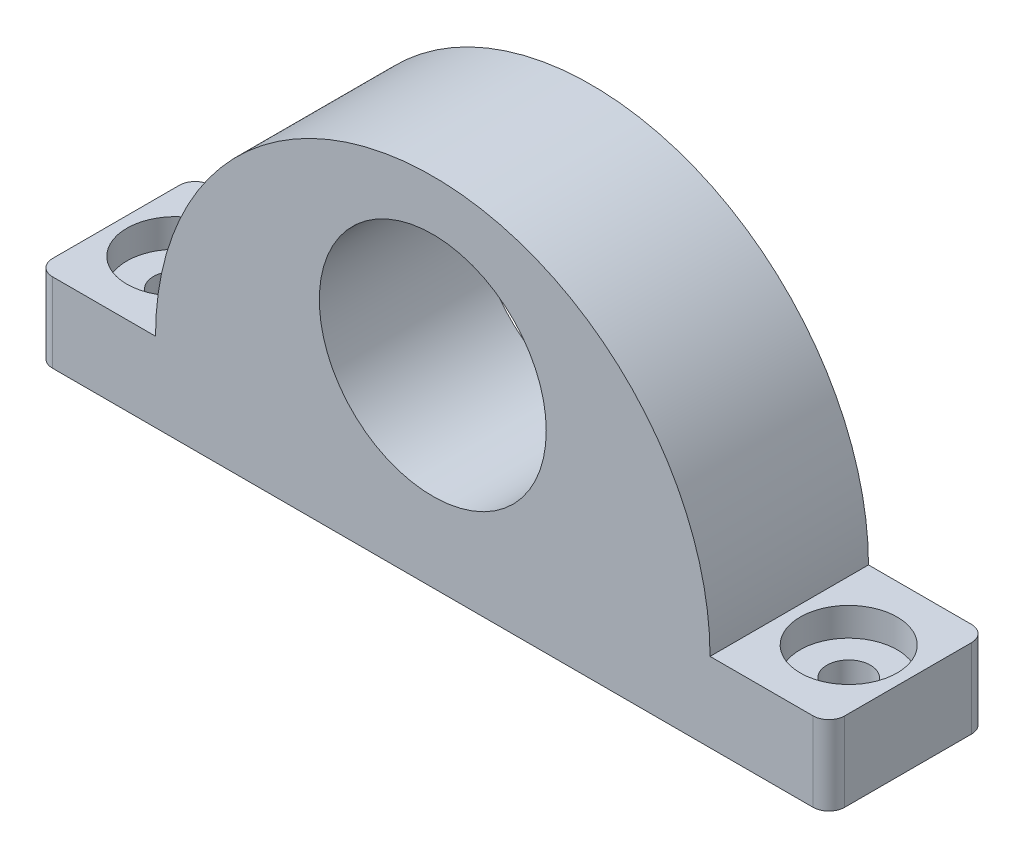
SolidWorks part; units mm, degrees
ref_plane "Front Plane" through (0, 0, 0) normal (0, 0, 1) x (1, 0, 0)
ref_plane "Top Plane" through (0, 0, 0) normal (0, 1, 0) x (1, 0, 0)
ref_plane "Right Plane" through (0, 0, 0) normal (1, 0, 0) x (0, 0, -1)
sketch "Sketch3" plane through (0, 0, 0) normal (0, 0, 1) x (1, 0, 0)
  line L0 (0, 19.325) -> (0, 0) construction
  line L2 (-35, 5) -> (-35, -5)
  line L3 (-35, -5) -> (35, -5)
  line L4 (35, 5) -> (35, -5)
  line L5 (35, 5) -> (50, 5)
  line L6 (-35, -5) -> (-50, -5)
  line L7 (-35, -5) -> (-35, 5)
  line L8 (-35, 5) -> (-50, 5)
  line L9 (-50, -5) -> (-50, 5)
  line L10 (50, -5) -> (50, 5)
  line L11 (35, -5) -> (50, -5)
  line L12 (35, -5) -> (35, 5)
  circle A1 centre (0, 19.325) radius 14.325
  arc A3 (35, 5) -> (-35, 5) centre (0, 5) ccw
  point P0 (0, 0)
  dimension "D3" = 28.65
  dimension "D1" = 70
  dimension "D2" = 10
  dimension "D5" = 5
  dimension "D6" = 15
extrude "Boss-Extrude3" add sketch "Sketch3" along normal blind 20
hole_wizard "CBORE for M5 Hex Head Bolt1" positions "Sketch4" profile "Sketch5" counterbore size "M5" standard "ANSI Metric" end condition up to next
sketch "Sketch4" plane through (0, 5, 0) normal (0, 1, 0) x (1, 0, 0)
  line L0 (-35, 0) -> (-50, 0) construction
  line L1 (-50, -20) -> (-50, 0) construction
  line L2 (50, -20) -> (50, 0) construction
  line L3 (35, -20) -> (50, -20) construction
  point P0 (-42.5, -10)
  point P2 (42.5, -10)
  dimension "D1" = 10
  dimension "D2" = 7.5
  dimension "D3" = 7.5
  dimension "D4" = 10
sketch "Sketch5" plane through (-42.5, 5, 10) normal (1, 0, 0) x (0, 0, 1)
  line L0 (0, 0) -> (0, 10)
  line L1 (0, 10) -> (2.75, 10)
  line L3 (2.75, 10) -> (2.75, 3.58)
  line L4 (2.75, 3.58) -> (6.12, 3.58)
  line L5 (6.12, 3.58) -> (6.12, 0)
  line L7 (6.12, 0) -> (0, 0)
  line L11 (0, -6.35) -> (0, 107.95) construction
  dimension "Thru Hole Dia." = 5.5
  dimension "Thru Hole Depth" = 10
  dimension "C'Bore Dia." = 12.24
  dimension "C'Bore Depth" = 3.58
fillet "Fillet1" radius 2 4 edges at (-50, 0, 0) (-50, 0, 20) (50, 0, 0) (50, 0, 20)
